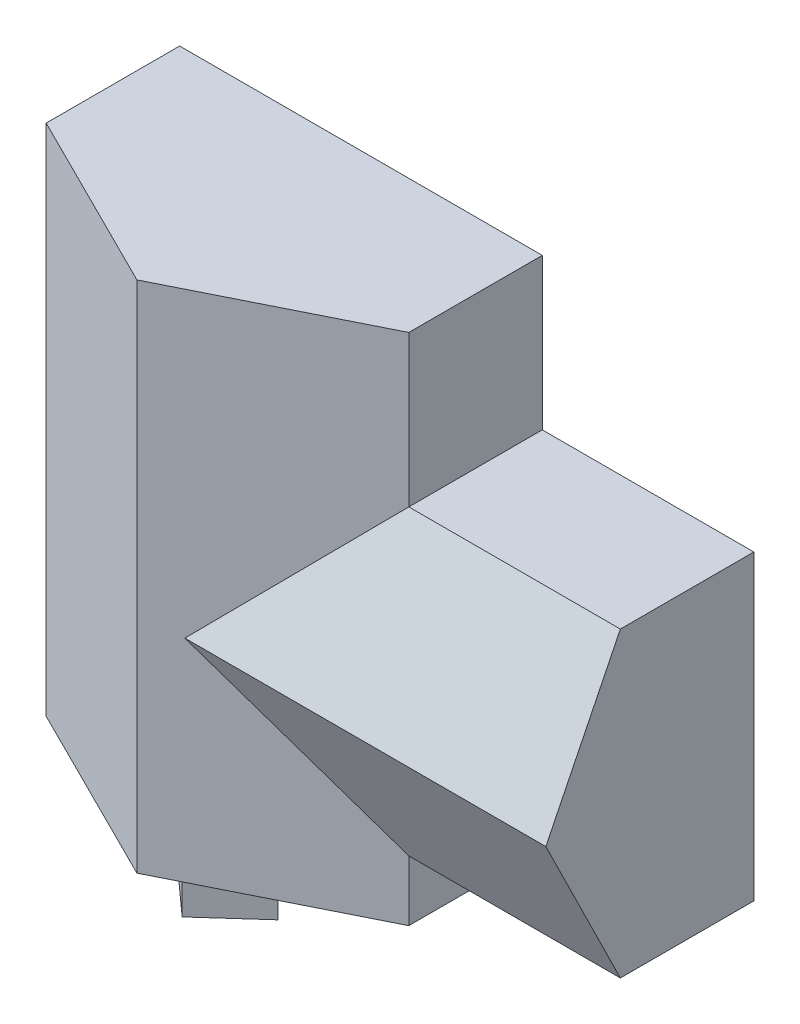
SolidWorks part; units mm, degrees
ref_plane "Front Plane" through (0, 0, 0) normal (0, 0, 1) x (1, 0, 0)
ref_plane "Top Plane" through (0, 0, 0) normal (0, 1, 0) x (1, 0, 0)
ref_plane "Right Plane" through (0, 0, 0) normal (1, 0, 0) x (0, 0, -1)
sketch "Sketch3" plane through (0, 0, 0) normal (0, 0, 1) x (1, 0, 0)
  line L0 (152.4, 152.4) -> (4550.005, 152.4)
  line L1 (0, 0) -> (11582.4, 0)
  line L2 (0, 0) -> (0, 6096)
  line L3 (0, 6096) -> (11582.4, 6096)
  line L4 (11582.4, 0) -> (11582.4, 6096)
  line L5 (4550.005, 152.4) -> (4550.005, 2596.7986)
  line L6 (4550.005, 2596.7986) -> (5842, 2596.7986)
  line L7 (11582.4, 6096) -> (7620, 6096) construction
  line L8 (7620, 6096) -> (5842, 6096) construction
  line L9 (5842, 5943.6) -> (5842, 3511.1986)
  line L10 (5943.6, 3511.1986) -> (10284.7543, 3511.1986)
  line L11 (7620, 5943.6) -> (7620, 3612.7986)
  line L12 (4550.005, 2596.7986) -> (5842, 2596.7986) construction
  line L13 (7315.2, 2495.1986) -> (7315.2, 152.4)
  line L14 (5842, 3511.1986) -> (5842, 2596.7986)
  line L15 (10386.3543, 3511.1986) -> (10386.3543, 2596.7986)
  line L16 (9786.5812, 3511.1986) -> (9786.5812, 2596.7986) construction
  line L17 (0, 6096) -> (0, 9448.8) construction
  line L18 (0, 9448.8) -> (6388.492, 9448.8) construction
  line L19 (6388.492, 9448.8) -> (6388.492, 6096) construction
  line L20 (11430, 152.4) -> (11430, 2495.1986)
  line L21 (3310.1163, 2590.8) -> (0, 2590.8) construction
  line L22 (152.4, 5943.6) -> (5842, 5943.6)
  line L23 (152.4, 152.4) -> (152.4, 5943.6)
  line L24 (4651.605, 152.4) -> (4651.605, 2495.1986)
  line L25 (4651.605, 2495.1986) -> (7315.2, 2495.1986)
  line L26 (7416.8, 2495.1986) -> (7416.8, 152.4)
  line L27 (10284.7543, 3511.1986) -> (10284.7543, 2596.7986)
  line L28 (5943.6, 3612.7986) -> (7620, 3612.7986)
  line L29 (5943.6, 5943.6) -> (5943.6, 3612.7986)
  line L30 (7721.6, 5943.6) -> (7721.6, 3612.7986)
  line L31 (7620, 6096) -> (7620, 3505.2) construction
  line L32 (7721.6, 6096) -> (7721.6, 3505.2) construction
  line L33 (5842, 6096) -> (5842, 3511.1986) construction
  line L34 (5943.6, 6096) -> (5943.6, 3511.1986) construction
  line L35 (5943.6, 5943.6) -> (7620, 5943.6)
  line L36 (152.4, 5943.6) -> (11430, 5943.6) construction
  line L37 (7721.6, 5943.6) -> (11430, 5943.6)
  line L38 (5842, 3612.7986) -> (11582.4, 3612.7986) construction
  line L39 (7721.6, 3612.7986) -> (11430, 3612.7986)
  line L40 (11430, 3612.7986) -> (11430, 5943.6)
  line L41 (11430, 152.4) -> (11430, 5943.6) construction
  line L42 (5842, 3511.1986) -> (11582.4, 3511.1986) construction
  line L43 (10386.3543, 3511.1986) -> (11430, 3511.1986)
  line L44 (10386.3543, 2596.7986) -> (11430, 2596.7986)
  line L45 (4550.005, 2596.7986) -> (11582.4, 2596.7986) construction
  line L46 (11430, 2596.7986) -> (11430, 3511.1986)
  line L47 (4651.605, 2495.1986) -> (11582.4, 2495.1986) construction
  line L48 (7315.2, 2596.7986) -> (7315.2, 0) construction
  line L49 (7416.8, 2596.7986) -> (7416.8, 0) construction
  line L50 (7416.8, 2495.1986) -> (11430, 2495.1986)
  line L51 (7416.8, 152.4) -> (11430, 152.4)
  line L52 (152.4, 152.4) -> (11430, 152.4) construction
  line L53 (4550.005, 0) -> (4550.005, 2596.7986) construction
  line L54 (4651.605, 0) -> (4651.605, 2495.1986) construction
  line L55 (4651.605, 152.4) -> (7315.2, 152.4)
  line L56 (5943.6, 3511.1986) -> (5943.6, 2596.7986)
  line L57 (5943.6, 2596.7986) -> (10284.7543, 2596.7986)
  line L58 (5943.6, 2596.7986) -> (7315.2, 2596.7986) construction
  dimension "D1" = 11582.4
  dimension "D2" = 6096
  dimension "D4" = 3962.4
  dimension "D5" = 1778
  dimension "D7" = 914.4
  dimension "D8" = 152.4
  dimension "D9" = 101.6
  dimension "D10" = 101.6
  dimension "D11" = 101.6
  dimension "D12" = 101.6
  dimension "D13" = 101.6
extrude "Boss-Extrude1" add sketch "Sketch3" along normal blind 2438.4 contours L1 L4 L3 L2 L55 L24 L25 L13 L51 L26 L50 L20 L46 L44 L15 L43 L40 L39 L30 L37 L10 L27 L6 L5 L0 L23 L22 L9 L29 L35 L11 L28
sketch "Sketch4" plane through (0, 0, 0) normal (0, 0, -1) x (-1, 0, 0)
  line L1 (-11582.4, 6096) -> (0, 6096)
  line L2 (-11582.4, 6096) -> (-11582.4, 0)
  line L3 (-11582.4, 0) -> (0, 0)
  line L4 (0, 6096) -> (0, 0)
extrude "Boss-Extrude2" add sketch "Sketch4" along normal blind 254
sketch "Sketch5" plane through (0, 0, 0) normal (0, 0, 1) x (1, 0, 0)
  line L1 (3330.805, 2596.7986) -> (152.4, 2596.7986)
  line L2 (152.4, 152.4) -> (152.4, 5943.6) construction
  line L3 (152.4, 2596.7986) -> (152.4, 2495.1986)
  line L4 (152.4, 152.4) -> (152.4, 5943.6) construction
  line L5 (152.4, 2495.1986) -> (3330.805, 2495.1986)
  line L6 (3330.805, 2495.1986) -> (3330.805, 2596.7986)
extrude "Boss-Extrude3" add sketch "Sketch5" along normal blind 1016
sketch "Sketch6" plane through (0, 0, 0) normal (-1, 0, 0) x (0, 0, 1)
  line L0 (2438.4, 6096) -> (2438.4, 0)
  line L1 (2438.4, 6096) -> (3941.5073, 3048)
  line L2 (2438.4, 3048) -> (3941.5073, 3048) construction
  line L3 (3941.5073, 3048) -> (2438.4, 0)
  dimension "D1" = 26.25
extrude "Boss-Extrude4" add sketch "Sketch6" against normal up to surface (11582.4 mm away) up to face at (11582.4, 3048, 1092.2)
sketch "Sketch7" plane through (0, 6096, 0) normal (0, 1, 0) x (1, 0, 0)
  line L0 (0, 254) -> (7315.2, 254) construction
  line L1 (0, 254) -> (11582.4, 254) construction
  line L2 (7315.2, 254) -> (7315.2, -2438.4) construction
  line L3 (0, -2438.4) -> (11582.4, -2438.4) construction
  line L4 (7937.8596, -2438.4) -> (5791.2, -3941.5073)
  line L5 (11582.4, -3941.5073) -> (0, -3941.5073) construction
  line L6 (5791.2, -3941.5073) -> (5791.2, -2438.4) construction
  line L7 (3644.5404, -2438.4) -> (5791.2, -3941.5073)
  line L8 (7937.8596, -2438.4) -> (3644.5404, -2438.4)
  dimension "D1" = 55
sketch "Sketch8" plane through (0, 0, -254) normal (0, 0, -1) x (-1, 0, 0)
  line L1 (0, 6096) -> (-7315.2, 6096)
  line L2 (0, 6096) -> (0, 9144)
  line L3 (0, 9144) -> (-7315.2, 9144)
  line L4 (-7315.2, 6096) -> (-7315.2, 9144)
  dimension "D1" = 7315.2
  dimension "D2" = 3048
extrude "Boss-Extrude6" add sketch "Sketch8" against normal blind 254 separate body
sketch "Sketch9" plane through (0, 0, 0) normal (-1, 0, 0) x (0, 0, 1)
  line L0 (2438.4, 0) -> (4693.0609, 4572)
  line L1 (2438.4, 0) -> (2438.4, 9144)
  line L2 (2438.4, 4572) -> (4693.0609, 4572) construction
  line L3 (2438.4, 9144) -> (4693.0609, 4572)
sketch "Sketch10" plane through (0, 9144, 0) normal (0, 1, 0) x (1, 0, 0)
  line L0 (7315.2, -2438.4) -> (0, -2438.4)
  line L1 (3644.5404, -2438.4) -> (3657.6, -4693.0609) construction
  line L2 (7315.2, -4693.0609) -> (0, -4693.0609) construction
  line L5 (7315.2, -2438.4) -> (3655.1104, -4263.2533)
  line L6 (3655.1104, -4263.2533) -> (0, -2438.4)
  dimension "D1" = 26.5
extrude "Boss-Extrude7" add sketch "Sketch10" against normal blind 10363.2
sketch "Sketch11" plane through (0, -967.2564, 1961.4019) normal (0, -0.4423, 0.8969) x (1, 0, 0)
  line L1 (5444.9184, 4256.1108) -> (2083.927, 4256.1108)
  line L2 (5444.9184, 4256.1108) -> (5444.9184, 5301.5124)
  line L3 (5444.9184, 5301.5124) -> (2083.927, 5301.5124)
  line L4 (2083.927, 4256.1108) -> (2083.927, 5301.5124)
extrude "Cut-Extrude1" [suppressed] cut sketch "Sketch11" along normal blind 6085.84
sketch "Sketch12" plane through (0, 0, -254) normal (0, 0, -1) x (-1, 0, 0)
  line L0 (0, 0) -> (0, -1219.2)
  line L1 (0, -1219.2) -> (-7315.2, -1219.2)
  line L2 (-7315.2, -1219.2) -> (-7315.2, 0)
  line L3 (-11582.4, 0) -> (0, 0) construction
  line L4 (-7315.2, 0) -> (0, 0)
extrude "Boss-Extrude8" add sketch "Sketch12" against normal blind 2692.4
sketch "Sketch14" plane through (0, 0, 0) normal (-1, 0, 0) x (0, 0, 1)
  line L0 (2916.7919, -235.9168) -> (4419.8992, 2812.0832)
  line L1 (2916.7919, -235.9168) -> (2299.5618, -1487.5356)
  line L2 (4419.8992, 2812.0832) -> (4384.9984, -1487.5356)
  line L3 (4384.9984, -1487.5356) -> (2299.5618, -1487.5356)
  line L6 (-254, 6096) -> (-254, -1219.2)
  line L7 (-254, -1219.2) -> (2438.4, -1219.2)
  line L8 (2438.4, -1219.2) -> (2438.4, 0)
  line L9 (2438.4, 0) -> (3941.5073, 3048)
  line L10 (3941.5073, 3048) -> (2438.4, 6096)
  line L11 (2438.4, 6096) -> (-254, 6096)
  line L15 (2438.4, 0) -> (3941.5073, 3048) construction
  dimension "D1" = 0
  dimension "D2" = 533.4
extrude "Cut-Extrude2" [suppressed] cut sketch "Sketch14" against normal blind 8897.366
sketch "Sketch15" plane through (0, -1219.2, 0) normal (0, -1, 0) x (1, 0, 0)
  line L0 (0, 2438.4) -> (7315.2, 2438.4) construction
  line L1 (3657.6, 2438.4) -> (3657.6, 3352.8) construction
  line L2 (2641.6, 2438.4) -> (4673.6, 2438.4)
  line L3 (4673.6, 2438.4) -> (3657.6, 3352.8)
  line L4 (3657.6, 3352.8) -> (2641.6, 2438.4)
  point P9 (3657.6, 2438.4)
extrude "Boss-Extrude9" add sketch "Sketch15" along normal blind 1219.2
ref_plane "Plane1" through (0, -1205.7554, 2445.0301) normal (0, -0.4423, 0.8969) x (1, 0, 0)
sketch "Sketch16" plane through (0, -1205.7554, 2445.0301) normal (0, -0.4423, 0.8969) x (1, 0, 0)
  line L1 (7603.0974, 4283.6963) -> (-536.5988, 4283.6963)
  line L2 (7603.0974, 4283.6963) -> (7603.0974, -1196.5845)
  line L3 (7603.0974, -1196.5845) -> (-536.5988, -1196.5845)
  line L4 (-536.5988, 4283.6963) -> (-536.5988, -1196.5845)
extrude "Cut-Extrude3" [suppressed] cut sketch "Sketch16" along normal blind 2099.564
sketch "Sketch17" plane through (7315.2, 0, 0) normal (1, 0, 0) x (0, 0, -1)
  line L0 (-2438.4, -1219.2) -> (-4263.2533, 0)
  line L1 (-4263.2533, -1219.2) -> (-4263.2533, 9144) construction
  line L2 (-4263.2533, 0) -> (-4263.2533, -2438.4)
  line L3 (-4263.2533, -2438.4) -> (-2438.4, -2438.4)
  line L4 (-2438.4, -2438.4) -> (-2438.4, -1219.2)
extrude "Cut-Extrude4" [suppressed] cut sketch "Sketch17" against normal blind 7574.28
sketch "Sketch18" plane through (-974.4939, 0, 1951.8734) normal (-0.4467, 0, 0.8947) x (0.8947, 0, 0.4467)
  line L1 (4842.2001, 6311.4159) -> (-249.1354, 6311.4159)
  line L2 (4842.2001, 6311.4159) -> (4842.2001, -413.9402)
  line L3 (4842.2001, -413.9402) -> (-249.1354, -413.9402)
  line L4 (-249.1354, 6311.4159) -> (-249.1354, -413.9402)
extrude "Cut-Extrude5" cut sketch "Sketch18" along normal blind 7574.28
sketch "Sketch19" plane through (0, 0, 0) normal (0, -1, 0) x (1, 0, 0)
  line L0 (11582.4, 2438.4) -> (9610.2834, 3941.5073)
  line L1 (11582.4, 3941.5073) -> (4300.4332, 3941.5073) construction
  line L2 (9610.2834, 3941.5073) -> (11582.4, 3941.5073)
  line L3 (11582.4, 3941.5073) -> (11582.4, 2438.4)
extrude "Cut-Extrude6" [suppressed] cut sketch "Sketch19" against normal blind 7574.28
sketch "Sketch20" plane through (0, 6096, 0) normal (0, 1, 0) x (1, 0, 0)
  line L1 (0, 0) -> (7315.2, 0)
  line L2 (0, 0) -> (0, -2438.4)
  line L3 (0, -2438.4) -> (7315.2, -2438.4)
  line L4 (7315.2, 0) -> (7315.2, -2438.4)
extrude "Boss-Extrude10" add sketch "Sketch20" along normal up to surface (3048 mm away) up to face at (3657.6, 9144, -127)
sketch "Sketch21" plane through (0, 9144, 0) normal (0, 1, 0) x (1, 0, 0)
  line L0 (7315.2, -2438.4) -> (0, -2438.4)
  line L1 (3657.6, -2438.4) -> (3655.1104, -4263.2533) construction
  line L2 (3655.1104, -4263.2533) -> (3655.1104, -4568.0533) construction
  line L3 (7315.2, -2438.4) -> (3655.1104, -4872.8533)
  line L4 (3655.1104, -4872.8533) -> (0, -2438.4)
  line L5 (3655.1104, -4568.0533) -> (3655.1104, -4872.8533) construction
  line L6 (3655.1104, -4872.8533) -> (3655.1104, -5177.6533) construction
  line L7 (3655.1104, -5177.6533) -> (3655.1104, -5482.4533) construction
  line L8 (3655.1104, -5482.4533) -> (3655.1104, -5787.2533) construction
  line L9 (3655.1104, -5787.2533) -> (3655.1104, -6092.0533) construction
  line L10 (7315.2, -2438.4) -> (3655.1104, -4568.0533) construction
  line L11 (3655.1104, -4568.0533) -> (0, -2438.4) construction
  line L12 (7315.2, -2438.4) -> (3655.1104, -5177.6533) construction
  line L13 (3655.1104, -5177.6533) -> (0, -2438.4) construction
  line L14 (7315.2, -2438.4) -> (3655.1104, -5482.4533) construction
  line L15 (3655.1104, -5482.4533) -> (0, -2438.4) construction
  line L16 (7315.2, -2438.4) -> (3655.1104, -5787.2533) construction
  line L17 (3655.1104, -5787.2533) -> (0, -2438.4) construction
  line L18 (7315.2, -2438.4) -> (3655.1104, -6092.0533) construction
  line L19 (3655.1104, -6092.0533) -> (0, -2438.4) construction
extrude "Boss-Extrude11" [suppressed] add sketch "Sketch21" against normal up to surface (10363.2 mm away)
sketch "Sketch22" [suppressed] plane through (0, 0, -254) normal (0, 0, -1) x (-1, 0, 0)
  line L1 (0, -1219.2) -> (-7298.2822, -1219.2)
  line L2 (0, -1219.2) -> (0, 5153.5416)
  line L3 (0, 5153.5416) -> (-7298.2822, 5153.5416)
  line L4 (-7298.2822, -1219.2) -> (-7298.2822, 5153.5416)
